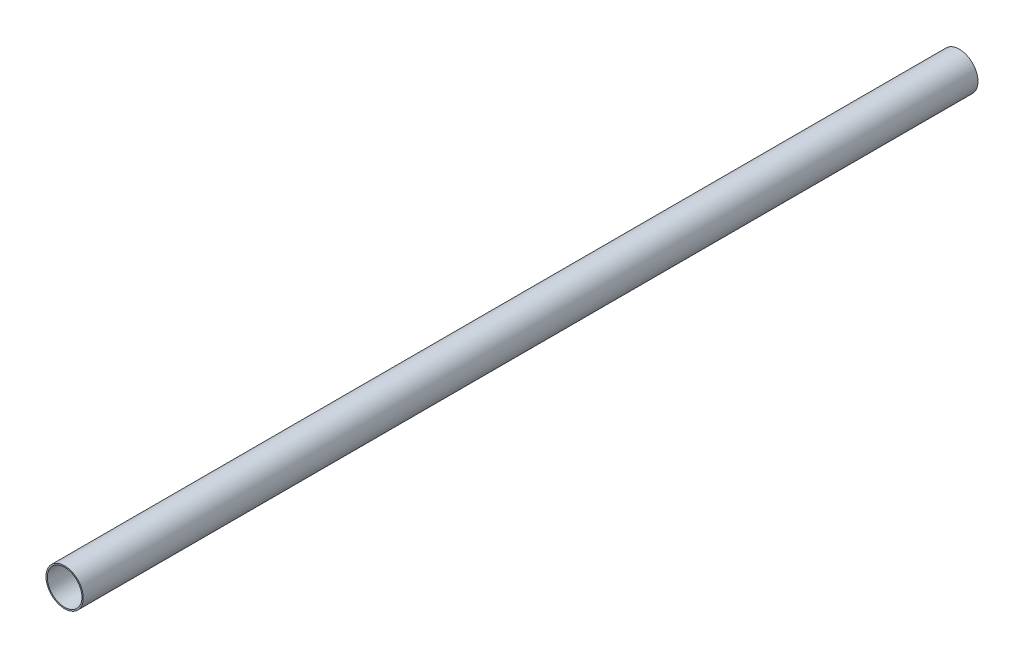
SolidWorks part; units mm, degrees
material "AISI 304"
ref_plane "Front Plane" through (0, 0, 0) normal (0, 0, 1) x (1, 0, 0)
ref_plane "Top Plane" through (0, 0, 0) normal (0, 1, 0) x (1, 0, 0)
ref_plane "Right Plane" through (0, 0, 0) normal (1, 0, 0) x (0, 0, -1)
sketch "Sketch1" plane through (0, 0, 0) normal (0, 0, 1) x (1, 0, 0)
  circle A0 centre (0, 0) radius 6.35
  circle A1 centre (0, 0) radius 5.9055
  dimension "D1" = 12.7
  dimension "D2" = 11.811
extrude "Boss-Extrude1" add sketch "Sketch1" along normal blind 304.8
